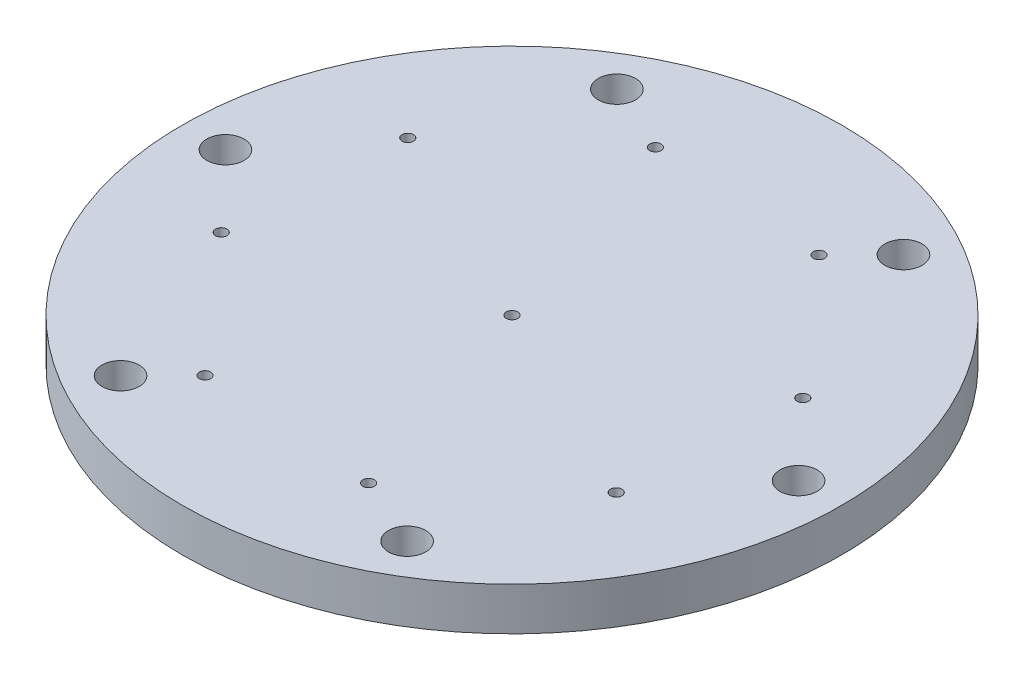
SolidWorks part; units mm, degrees
ref_plane "Front Plane" through (0, 0, 0) normal (0, 0, 1) x (1, 0, 0)
ref_plane "Top Plane" through (0, 0, 0) normal (0, 1, 0) x (1, 0, 0)
ref_plane "Right Plane" through (0, 0, 0) normal (1, 0, 0) x (0, 0, -1)
sketch "Sketch1" plane through (0, 0, 0) normal (0, 1, 0) x (1, 0, 0)
  line L0 (0, 0) -> (-50, 86.6025) construction
  line L1 (100, 0) -> (50, 86.6025) construction
  line L2 (50, 86.6025) -> (-50, 86.6025) construction
  line L3 (-50, 86.6025) -> (-100, 0) construction
  line L4 (-100, 0) -> (-50, -86.6025) construction
  line L5 (-50, -86.6025) -> (50, -86.6025) construction
  line L6 (50, -86.6025) -> (100, 0) construction
  line L8 (0, 0) -> (-25.7152, 75.7544) construction
  circle A17 centre (0, 0) radius 115
  circle A18 centre (0, 0) radius 65
  circle A21 centre (0, 0) radius 86.6025 construction
  circle A22 centre (50, 86.6025) radius 6.5
  circle A23 centre (100, 0) radius 6.5
  circle A24 centre (50, -86.6025) radius 6.5
  circle A25 centre (-50, -86.6025) radius 6.5
  circle A26 centre (-100, 0) radius 6.5
  circle A27 centre (-50, 86.6025) radius 6.5
  circle A35 centre (-25.7152, 75.7544) radius 2
  circle A36 centre (35.3831, 71.7498) radius 2
  circle A37 centre (75.7544, 25.7152) radius 2
  circle A38 centre (71.7498, -35.3831) radius 2
  circle A39 centre (25.7152, -75.7544) radius 2
  circle A40 centre (-35.3831, -71.7498) radius 2
  circle A41 centre (-75.7544, -25.7152) radius 2
  circle A42 centre (-71.7498, 35.3831) radius 2
  point P35 (0, 0)
  point P37 (0, 0)
  dimension "D1" = 230
  dimension "D2" = 130
  dimension "D3" = 11.25
  dimension "D5" = 4
  dimension "D7" = 13
  dimension "D4" = 80
  dimension "D6" = 200
  dimension "D8" = 8
extrude "Boss-Extrude1" add sketch "Sketch1" along normal blind 15
sketch "Sketch2" plane through (0, 15, 0) normal (0, 1, 0) x (1, 0, 0)
  circle A0 centre (0, 0) radius 65
extrude "Boss-Extrude2" add sketch "Sketch2" against normal blind 5
sketch "Sketch4" plane through (0, 10, 0) normal (0, -1, 0) x (1, 0, 0)
  circle A0 centre (0, 0) radius 2
  dimension "D1" = 4
extrude "Cut-Extrude1" cut sketch "Sketch4" against normal up to surface (5 mm away) up to face at (-75.7544, 15, 27.7152)
